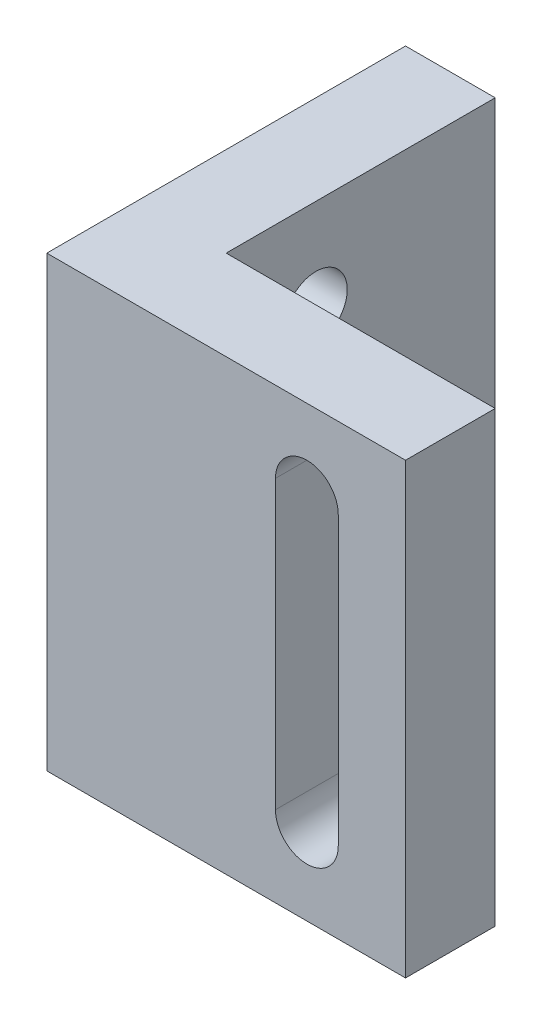
SolidWorks part; units mm, degrees
ref_plane "Front Plane" through (0, 0, 0) normal (0, 0, 1) x (1, 0, 0)
ref_plane "Top Plane" through (0, 0, 0) normal (0, 1, 0) x (1, 0, 0)
ref_plane "Right Plane" through (0, 0, 0) normal (1, 0, 0) x (0, 0, -1)
sketch "Sketch1" plane through (0, 0, 0) normal (0, 1, 0) x (1, 0, 0)
  line L0 (-5, 15) -> (-5, -5)
  line L1 (-5, -5) -> (15, -5)
  line L2 (15, -5) -> (15, 0)
  line L3 (15, 0) -> (0, 0)
  line L4 (0, 0) -> (0, 15)
  line L5 (0, 15) -> (-5, 15)
  point P6 (3.6685, -1.8207)
  point P7 (13.125, 1.3859)
  point P8 (0, 0)
  dimension "D1" = 20
  dimension "D2" = 20
  dimension "D3" = 5
  dimension "D4" = 5
extrude "Boss-Extrude1" add sketch "Sketch1" along normal blind 25
sketch "Sketch2" plane through (0, 0, 0) normal (0, 0, -1) x (-1, 0, 0)
  line L0 (-9.5, 25) -> (-9.5, 0) construction
  line L1 (-15, 25) -> (0, 25) construction
  line L2 (-15, 0) -> (0, 0) construction
  line L4 (5, 25) -> (5, 0) construction
  line L5 (5, 25) -> (5, 0) construction
  line L6 (-15, 12.5) -> (5, 12.5) construction
  line L7 (-15, 25) -> (-15, 0) construction
  line L8 (-9.5, 20.5) -> (-9.5, 4.5) construction
  line L9 (-7.75, 20.5) -> (-7.75, 4.5)
  line L10 (-11.25, 20.5) -> (-11.25, 4.5)
  arc A2 (-7.75, 20.5) -> (-11.25, 20.5) centre (-9.5, 20.5) ccw
  arc A3 (-11.25, 4.5) -> (-7.75, 4.5) centre (-9.5, 4.5) ccw
  point P16 (-9.5, 12.5)
  dimension "D1" = 1.75
  dimension "D2" = 14.5
  dimension "D3" = 8
extrude "Cut-Extrude1" cut sketch "Sketch2" against normal up to surface (5 mm away) up to face at (5, 12.5, 5)
sketch "Sketch3" plane through (-5, 0, 0) normal (-1, 0, 0) x (0, 0, 1)
  line L0 (-15, 12.5) -> (5, 12.5) construction
  line L1 (-15, 25) -> (-15, 0) construction
  line L2 (5, 25) -> (5, 0) construction
  circle A0 centre (-5, 5.134) radius 1.75
  circle A1 centre (-5, 19.866) radius 1.75
  dimension "D1" = 3.5
  dimension "D2" = 7.366
  dimension "D3" = 10
extrude "Cut-Extrude2" cut sketch "Sketch3" against normal up to surface (5 mm away) up to face at (0, 12.5, -7.5)
